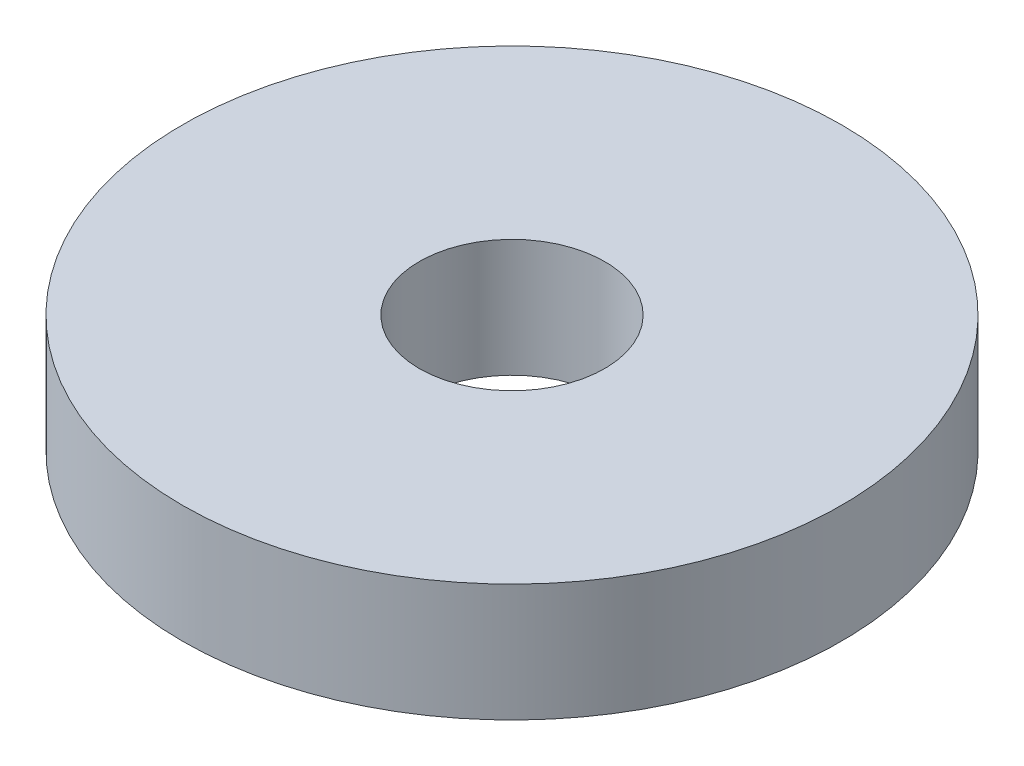
SolidWorks part; units mm, degrees
ref_plane "Front Plane" through (0, 0, 0) normal (0, 0, 1) x (1, 0, 0)
ref_plane "Top Plane" through (0, 0, 0) normal (0, 1, 0) x (1, 0, 0)
ref_plane "Right Plane" through (0, 0, 0) normal (1, 0, 0) x (0, 0, -1)
sketch "Sketch1" plane through (0, 0, 0) normal (0, 1, 0) x (1, 0, 0)
  circle A0 centre (0, 0) radius 2.5019
  circle A1 centre (0, 0) radius 8.89
  dimension "D1" = 5.0038
  dimension "D2" = 17.78
extrude "Boss-Extrude1" add sketch "Sketch1" along normal blind 3.175
